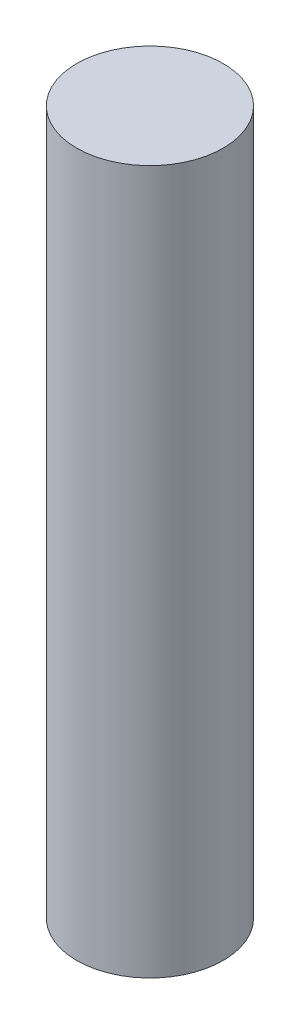
SolidWorks part; units mm, degrees
ref_plane "Front Plane" through (0, 0, 0) normal (0, 0, 1) x (1, 0, 0)
ref_plane "Top Plane" through (0, 0, 0) normal (0, 1, 0) x (1, 0, 0)
ref_plane "Right Plane" through (0, 0, 0) normal (1, 0, 0) x (0, 0, -1)
sketch "Sketch1" plane through (0, 0, 0) normal (0, 1, 0) x (1, 0, 0)
  circle A0 centre (0, 0) radius 7.5
  dimension "D1" = 15
extrude "Boss-Extrude1" add sketch "Sketch1" along normal blind 72
